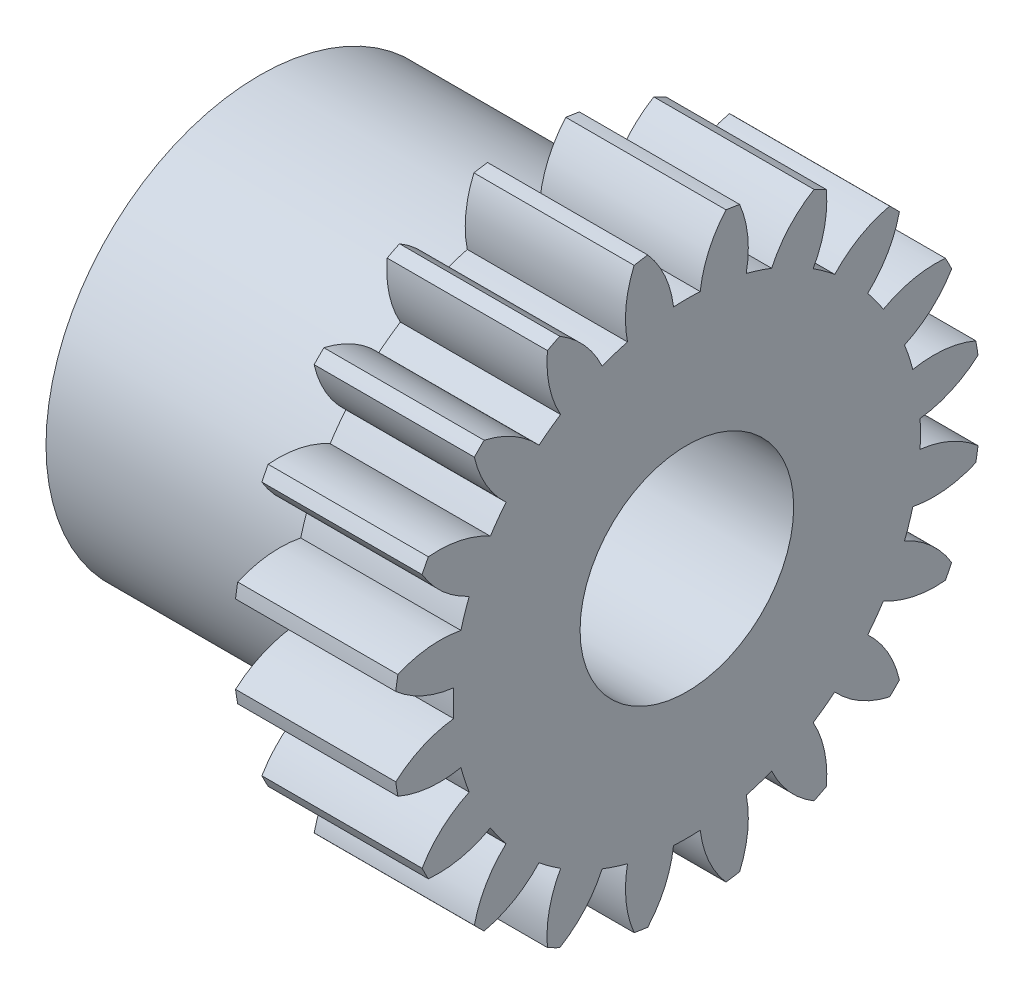
SolidWorks part; units mm, degrees
ref_plane "Plane1" through (0, 0, 0) normal (0, 0, 1) x (1, 0, 0)
ref_plane "Plane2" through (0, 0, 0) normal (0, 1, 0) x (1, 0, 0)
ref_plane "Plane3" through (0, 0, 0) normal (1, 0, 0) x (0, 0, -1)
sketch "HoldingSke" plane through (0, 0, 0) normal (0, 1, 0) x (1, 0, 0)
  line L0 (0, 0) -> (1.8794, -0.684)
  line L1 (-15, 0) -> (100, 0) construction
  line L2 (0, 0) -> (-2.1039, 2.3779)
  line L3 (0, 0) -> (-11.863, 4.5341)
  line L4 (0, 0) -> (8.1152, 2.9537)
  line L5 (0, 0) -> (-7.4956, -2.7956)
  line L6 (0, 0) -> (-2.4869, -1.6779)
  line L7 (-2.1039, 2.3779) -> (-0.3819, 10.1904)
  line L8 (-76.2, 54.61) -> (-75.5, 54.61)
  line L9 (-71.009, 38.7566) -> (-53.1078, 45.2721)
  line L10 (-76.2, 71.12) -> (104.1128, 71.12)
  line L11 (0, 0) -> (-3, 0)
  line L12 (-76.2, 101.6) -> (-76.181, 101.6)
  line L13 (24.9733, 27.94) -> (52.9518, 28.4284)
  line L14 (24.9733, 27.94) -> (24.9743, 27.94)
  line L15 (24.9733, 27.94) -> (100.4006, 29.5858)
  line L16 (-63.627, -0.5) -> (-12.827, -0.5)
  circle A0 centre (0, 0) radius 2
  circle A1 centre (0, 0) radius 4
  circle A2 centre (0, 0) radius 4
  circle A3 centre (0, 0) radius 2
  dimension "MHD" = 8
  dimension "Hub_dia" = 8
  dimension "Bore" = 4
  dimension "MBD" = 4
  dimension "Num_teeth" = 20
  dimension "Pitch_radius" = 180.3128
  dimension "Pitch" = 2
  dimension "Width" = 3
  dimension "Overall_len" = 8
  dimension "Show_teeth" = 20
  dimension "Thickness" = 3
  dimension "OAL" = 8.0001
  dimension "T_dim" = 0.7
  dimension "Ap" = 20
  dimension "H" = 19.05
  dimension "Backlash" = 0.019
  dimension "Addendum_fac" = 1
  dimension "Dedendum_fac" = 1.25
  dimension "Clearance_fac" = 0.25
  dimension "Dedendum_add" = 0.001
  dimension "Module" = 0.5
sketch "BasProSke" plane through (0, 0, 0) normal (0, 1, 0) x (1, 0, 0)
  line L0 (-10, 0) -> (60, 0) construction
  line L1 (0, 0) -> (0, 5.5)
  line L2 (0, 0) -> (3, 0)
  line L3 (3, 0) -> (3, 5.5)
  line L4 (3, 5.5) -> (0, 5.5)
  dimension "Diameter" = 11
  dimension "Thickness" = 3
revolve "Base-Revolve" add sketch "BasProSke" angle 360 about L0
sketch "TooCutSke" plane through (0, 0, 0) normal (1, 0, 0) x (0, 0, -1)
  line L1 (0, 0) -> (0, 107) construction
  line L2 (0, 0) -> (-0.4255, 4.9819) construction
  line L3 (0, 0) -> (-1.5603, 9.8514) construction
  line L4 (-0.4255, 4.9819) -> (-0.7802, 4.9257) construction
  arc A0 (0.2499, 4.3669) -> (-0.2499, 4.3669) centre (0, 0) ccw
  arc A1 (0.7528, 5.4739) -> (-0.7528, 5.4739) centre (0, 0) ccw
  circle A2 centre (0, 0) radius 5 construction
  circle A3 centre (0, 0) radius 4.6985 construction
  arc A4 (-0.2499, 4.3669) -> (-0.7528, 5.4739) centre (-2.2361, 4.1322) ccw
  arc A5 (0.7528, 5.4739) -> (0.2499, 4.3669) centre (2.2361, 4.1322) ccw
  dimension "Root_dia" = 8.748
  dimension "Overcut_dia" = 11.0508
  dimension "Pitch_dia" = 10
  dimension "Base_dia" = 9.3969
  dimension "Flank_rad" = 2
  dimension "Half_ang" = 9
  dimension "Half_CT" = 0.359
extrude "ToothCut" cut sketch "TooCutSke" along normal through all
fillet "Breaks" [suppressed] radius 0.01
fillet "RootFillets" [suppressed] radius 0.126
pattern_circular "TeethCuts" count 20 every 18 about axis through (-10, 0, 0) along (1, 0, 0) of "ToothCut", "RootFillets", "Breaks"
sketch "HubNeaOneSke" plane through (0, 0, 0) normal (-1, 0, 0) x (0, 0, 1)
  circle A0 centre (0, 0) radius 4
  dimension "Diameter" = 8
extrude "HubNearOne" add sketch "HubNeaOneSke" along normal blind 5.0001
sketch "HubNeaBotSke" plane through (0, 0, 0) normal (-1, 0, 0) x (0, 0, 1)
  circle A0 centre (0, 0) radius 4
  dimension "Diameter" = 8
extrude "HubNearBoth" [suppressed] add sketch "HubNeaBotSke" along normal blind 2.5
ref_plane "FarPln" through (3, 0, 0) normal (1, 0, 0) x (0, 0, -1)
sketch "HubFarSke" plane through (3, 0, 0) normal (1, 0, 0) x (0, 0, -1)
  circle A0 centre (0, 0) radius 4
  dimension "Diameter" = 8
extrude "HubFar" [suppressed] add sketch "HubFarSke" along normal blind 2.5
sketch "BorSke" plane through (0, 0, 0) normal (1, 0, 0) x (0, 0, -1)
  circle A0 centre (0, 0) radius 2
  dimension "Diameter" = 4
extrude "Bore" cut sketch "BorSke" along normal mid plane 16.0001
sketch "KeySke" plane through (0, 0, 0) normal (1, 0, 0) x (0, 0, -1)
  line L0 (-0.8, 0) -> (-0.8, 2.7)
  line L1 (-0.8, 2.7) -> (0.8, 2.7)
  line L2 (0.8, 2.7) -> (0.8, 0)
  line L3 (0, 0) -> (0, 34) construction
  line L4 (-0.8, 0) -> (0.8, 0)
  dimension "Offset" = 2.7
  dimension "Width" = 1.6
extrude "Keyway" [suppressed] cut sketch "KeySke" along normal mid plane 16.0001
pattern_circular "Keyway2" [suppressed] count 2 every 90 about axis through (-10, 0, 0) along (1, 0, 0)
equation "' \"Module@HoldingSke\" = 6.35"
equation "' \"Num_teeth@HoldingSke\" = 12"
equation "' \"Ap@HoldingSke\" =  20"
equation "' \"Width@HoldingSke\" = 0.5 * 25.4"
equation "' \"Hub_dia@HoldingSke\"= 1 * 25.4"
equation "' \"Overall_len@HoldingSke\" = 1.0 * 25.4"
equation "' \"Bore@HoldingSke\" = 0.75 * 25.4"
equation "' \"T_dim@HoldingSke\" = 0.1 * 25.4"
equation "' \"Width@KeySke\" = 0.25 * 25.4"
equation "' \"Show_teeth@HoldingSke\" = 13"
equation "' \"Backlash@HoldingSke\" = 0.009 * 25.4"
equation "' \"Addendum_fac@HoldingSke\" = 1.0"
equation "' \"Dedendum_fac@HoldingSke\" = 1.25"
equation "' \"Dedendum_add@HoldingSke\" = 0.00005 * 25.4"
equation "' \"Clearance_fac@HoldingSke\" = 0.25"
equation "\"Pitch@HoldingSke\" = 1 / \"Module@HoldingSke\""
equation "\"Overcut_dia@TooCutSke\" = (\"Num_teeth@HoldingSke\" + 2 * \"Addendum_fac@HoldingSke\") / \"Pitch@HoldingSke\" + 0.002 * 25.4"
equation "\"Pitch_dia@TooCutSke\" = \"Num_teeth@HoldingSke\" / \"Pitch@HoldingSke\""
equation "\"Base_dia@TooCutSke\" = \"Num_teeth@HoldingSke\" / \"Pitch@HoldingSke\" * cos((\"Ap@HoldingSke\"  * 3.14159265 / 180))"
equation "\"Root_dia@TooCutSke\" = (\"Num_teeth@HoldingSke\" + 2) / \"Pitch@HoldingSke\" - 2 * (\"Addendum_fac@HoldingSke\" + \"Dedendum_fac@HoldingSke\") / \"Pitch@HoldingSke\" - \"Dedendum_add@HoldingSke\" * 2"
equation "\"Half_ang@TooCutSke\" = 180 / \"Num_teeth@HoldingSke\""
equation "\"Half_CT@TooCutSke\" = \"Num_teeth@HoldingSke\" / \"Pitch@HoldingSke\" * sin((3.14159265 / 2 / \"Num_teeth@HoldingSke\")) / 2 - 7 * \"Backlash@HoldingSke\" / 4"
equation "\"Flank_rad@TooCutSke\" = \"Num_teeth@HoldingSke\" / \"Pitch@HoldingSke\" / 5"
equation "\"Radius@RootFillets\" = \"Clearance_fac@HoldingSke\" / \"Pitch@HoldingSke\" + \"Dedendum_add@HoldingSke\""
equation "\"Break_rad@Breaks\" = 0.02 / \"Pitch@HoldingSke\""
equation "\"Thickness@HoldingSke\" = \"Width@HoldingSke\""
equation "\"OAL@HoldingSke\" = \"Thickness@HoldingSke\""
equation "\"MHD@HoldingSke\" = (\"Num_teeth@HoldingSke\" + 2) / \"Pitch@HoldingSke\" - 2 * (\"Addendum_fac@HoldingSke\" + \"Dedendum_fac@HoldingSke\")  / \"Pitch@HoldingSke\" - \"Dedendum_add@HoldingSke\" * 2"
equation "\"MBD@HoldingSke\" = (\"Num_teeth@HoldingSke\" + 2) / \"Pitch@HoldingSke\" - 2 * (\"Addendum_fac@HoldingSke\" + \"Dedendum_fac@HoldingSke\")  / \"Pitch@HoldingSke\" - \"Dedendum_add@HoldingSke\" * 2 - 0.002 * 25.4"
equation "\"MHD@HoldingSke\" = ((sgn( \"MHD@HoldingSke\" - \"Hub_dia@HoldingSke\" )-1)*( \"MHD@HoldingSke\" - \"Hub_dia@HoldingSke\" ))/-2+ \"Hub_dia@HoldingSke\""
equation "\"MBD@HoldingSke\" = ((sgn( \"MBD@HoldingSke\" - \"Bore@HoldingSke\" )-1)*( \"MBD@HoldingSke\" - \"Bore@HoldingSke\" ))/-2+ \"Bore@HoldingSke\""
equation "\"OAL@HoldingSke\" = ((sgn( \"OAL@HoldingSke\" - \"Overall_len@HoldingSke\" )+1)*( \"OAL@HoldingSke\" - \"Overall_len@HoldingSke\" ))/2 + \"Overall_len@HoldingSke\" + 0.000002 * 25.4"
equation "\"Num_teeth@TeethCuts\" = int( \"Show_teeth@HoldingSke\" ) + 1"
equation "\"Num_teeth@TeethCuts\" = ((sgn( \"Num_teeth@TeethCuts\" - \"Num_teeth@HoldingSke\" )-1)*( \"Num_teeth@TeethCuts\" - \"Num_teeth@HoldingSke\" ))/-2+ \"Num_teeth@HoldingSke\""
equation "\"Num_teeth@TeethCuts\" = ((sgn( \"Num_teeth@TeethCuts\" - 2.0)+1)*( \"Num_teeth@TeethCuts\" - 2.0))/2 +2.0"
equation "\"Angle@TeethCuts\" = 360.0 / \"Num_teeth@HoldingSke\""
equation "\"Diameter@BasProSke\" = (\"Num_teeth@HoldingSke\" + 2 * \"Addendum_fac@HoldingSke\") / \"Pitch@HoldingSke\""
equation "\"Thickness@BasProSke\"  = \"Thickness@HoldingSke\""
equation "' \"Fillet_rad@BasProSke\" =  \"Thickness@HoldingSke\" * 0.05"
equation "\"MHD@HoldingSke\" = ((sgn( \"MHD@HoldingSke\" - \"Root_dia@TooCutSke\" )-1)*( \"MHD@HoldingSke\" - \"Root_dia@TooCutSke\" ))/-2+ \"Root_dia@TooCutSke\""
equation "\"Diameter@HubNeaOneSke\" = \"MHD@HoldingSke\""
equation "\"Length@HubNearOne\" = \"OAL@HoldingSke\" - \"Thickness@BasProSke\""
equation "\"Diameter@HubNeaBotSke\" = \"MHD@HoldingSke\""
equation "\"Length@HubNearBoth\" = ( \"OAL@HoldingSke\" - \"Thickness@BasProSke\" ) / 2.0"
equation "\"Thickness@FarPln\" = \"Thickness@BasProSke\""
equation "\"Diameter@HubFarSke\" = \"MHD@HoldingSke\""
equation "\"Length@HubFar\" = ( \"OAL@HoldingSke\" - \"Thickness@BasProSke\" ) / 2.0"
equation "\"Diameter@BorSke\" = \"MBD@HoldingSke\""
equation "\"D1@Bore\" = \"OAL@HoldingSke\" * 2.0"
equation "\"D1@Keyway\" = \"OAL@HoldingSke\" * 2.0"
equation "\"Offset@KeySke\" = \"T_dim@HoldingSke\" + \"MBD@HoldingSke\" / 2.0"
